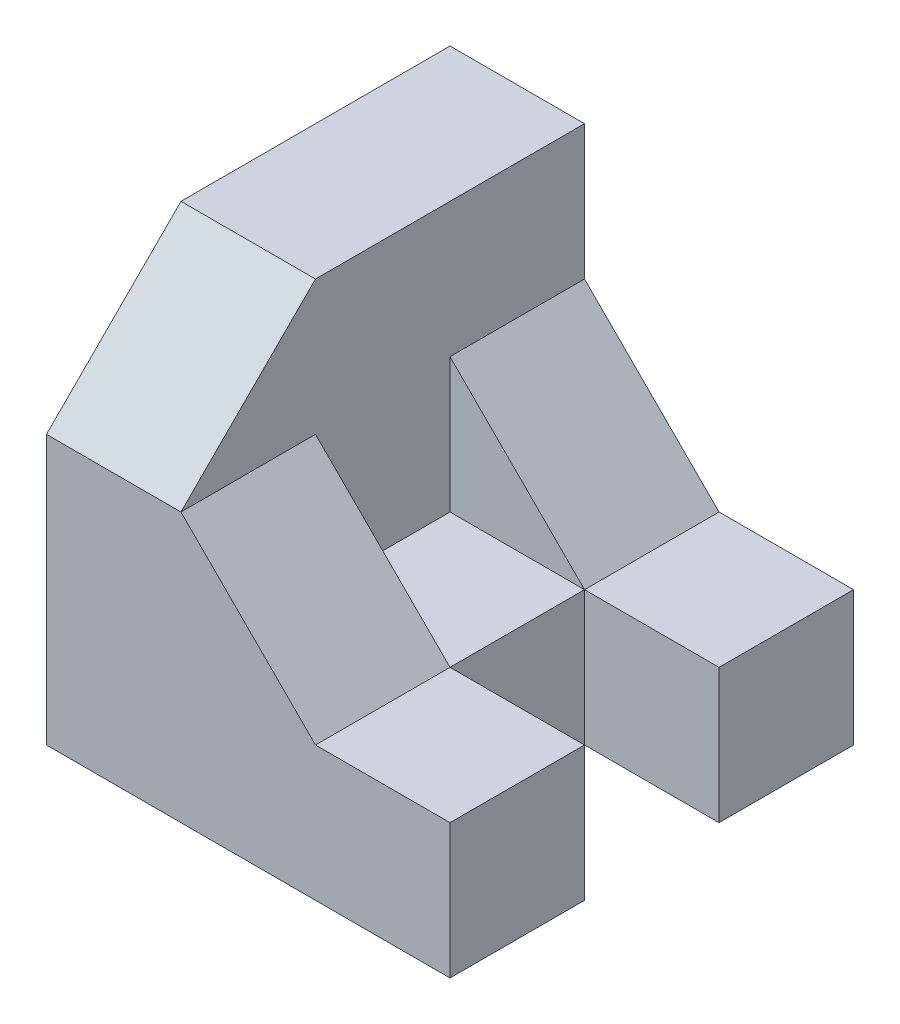
SolidWorks part; units mm, degrees
ref_plane "Alzado" through (0, 0, 0) normal (0, 0, 1) x (1, 0, 0)
ref_plane "Planta" through (0, 0, 0) normal (0, 1, 0) x (1, 0, 0)
ref_plane "Vista lateral" through (0, 0, 0) normal (1, 0, 0) x (0, 0, -1)
sketch "Croquis3" plane through (0, 0, 0) normal (0, 0, 1) x (1, 0, 0)
  line L0 (0, 0) -> (60, 0)
  line L1 (60, 0) -> (60, 20)
  line L2 (60, 20) -> (40, 20)
  line L3 (40, 20) -> (20, 40)
  line L4 (20, 40) -> (20, 60)
  line L5 (20, 60) -> (0, 60)
  line L6 (0, 60) -> (0, 0)
  point P7 (0, 0)
  dimension "D1" = 60
  dimension "D2" = 20
  dimension "D3" = 20
extrude "Saliente-Extruir1" add sketch "Croquis3" against normal blind 60
sketch "Croquis4" plane through (20, 0, 0) normal (1, 0, 0) x (0, 0, -1)
  line L0 (0, 40) -> (20, 60)
  line L1 (60, 60) -> (0, 60) construction
  line L2 (20, 60) -> (0, 60)
  line L3 (0, 40) -> (0, 60) construction
  line L4 (0, 60) -> (0, 40)
  dimension "D1" = 20
extrude "Cortar-Extruir1" cut sketch "Croquis4" against normal up to surface (20 mm away) up to face at (0, 30, -30)
ref_plane "Plano1" through (0, 0, -30) normal (0, 0, 1) x (1, 0, 0)
sketch "Croquis6" plane through (0, 0, -30) normal (0, 0, 1) x (1, 0, 0)
  line L0 (60, 0) -> (60, 20) construction
  line L1 (60, 20) -> (40, 20) construction
  line L2 (40, 20) -> (20, 40) construction
  line L3 (60, 0) -> (60, 20)
  line L4 (60, 20) -> (40, 20)
  line L5 (40, 20) -> (20, 40)
  line L6 (20, 40) -> (20, 20)
  line L7 (20, 20) -> (40, 20)
  line L8 (40, 0) -> (60, 0)
  line L9 (0, 0) -> (60, 0) construction
  line L10 (40, 20) -> (40, 0)
extrude "Cortar-Extruir3" cut sketch "Croquis6" against normal mid plane 20 contours L6 L7 L5 | L4 L10 L8 L3
